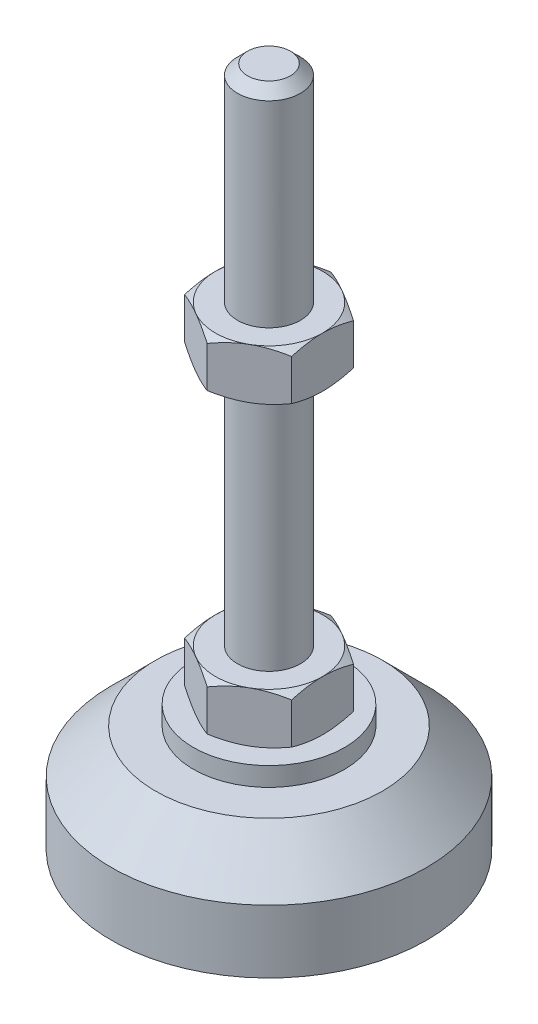
SolidWorks part; units mm, degrees
ref_plane "Спереди" through (0, 0, 0) normal (0, 0, 1) x (1, 0, 0)
ref_plane "Сверху" through (0, 0, 0) normal (0, 1, 0) x (1, 0, 0)
ref_plane "Справа" through (0, 0, 0) normal (1, 0, 0) x (0, 0, -1)
sketch "Эскиз1" plane through (0, 0, 0) normal (0, 0, 1) x (1, 0, 0)
  line L0 (0, 0) -> (-25, 0)
  line L3 (-25, 0) -> (-25, 10)
  line L5 (-12, 20) -> (-5, 20)
  line L12 (-5, 28) -> (-5, 106.4)
  line L13 (-5, 106.4) -> (-3.4, 108)
  line L14 (-3.4, 108) -> (0, 108)
  line L15 (0, 108) -> (0, 0) construction
  line L16 (-5, 20) -> (0, 20) construction
  line L17 (0, 0) -> (0, 108)
  line L18 (0, 0) -> (0, -7.9595) construction
  line L19 (-5, 28) -> (-5, 20)
  line L20 (-12, 20) -> (-12, 17)
  line L21 (-12, 17) -> (-18, 17)
  line L22 (-18, 17) -> (-25, 10)
  point P8 (-5, 67.2)
  point P23 (-8.5, 20)
  dimension "D1" = 10
  dimension "D2" = 20
  dimension "D3" = 8
  dimension "D4" = 50
  dimension "D5" = 5
  dimension "D6" = 1.6
  dimension "D7" = 45
  dimension "D8" = 24
  dimension "D10" = 80
  dimension "D11" = 10
  dimension "D12" = 45
  dimension "D13" = 3
revolve "Повернуть1" add sketch "Эскиз1" angle 360 about L17
sketch "Эскиз2" plane through (0, 20, 0) normal (0, 1, 0) x (1, 0, 0)
  line L1 (0, 9.815) -> (-8.5, 4.9075)
  line L2 (-8.5, 4.9075) -> (-8.5, -4.9075)
  line L3 (-8.5, -4.9075) -> (0, -9.815)
  line L4 (0, -9.815) -> (8.5, -4.9075)
  line L5 (8.5, -4.9075) -> (8.5, 4.9075)
  line L6 (8.5, 4.9075) -> (0, 9.815)
  circle A0 centre (0, 0) radius 8.5 construction
  dimension "D1" = 17
extrude "Бобышка-Вытянуть1" add sketch "Эскиз2" along normal up to vertex (8 mm away) up to point (-5, 28, 0)
ref_plane "Плоскость1" through (0, 67.2, 0) normal (0, 1, 0) x (1, 0, 0)
sketch "Эскиз3" plane through (0, 67.2, 0) normal (0, 1, 0) x (1, 0, 0)
  line L6 (8.5, 4.9075) -> (0, 9.815)
  line L7 (0, 9.815) -> (-8.5, 4.9075)
  line L8 (-8.5, 4.9075) -> (-8.5, -4.9075)
  line L9 (-8.5, -4.9075) -> (0, -9.815)
  line L10 (0, -9.815) -> (8.5, -4.9075)
  line L11 (8.5, -4.9075) -> (8.5, 4.9075)
  line L12 (8.5, 4.9075) -> (0, 9.815)
  line L13 (0, 9.815) -> (-8.5, 4.9075)
  line L14 (-8.5, 4.9075) -> (-8.5, -4.9075)
  line L15 (-8.5, -4.9075) -> (0, -9.815)
  line L16 (0, -9.815) -> (8.5, -4.9075)
  line L17 (8.5, -4.9075) -> (8.5, 4.9075)
  dimension "D1" = 0
extrude "Бобышка-Вытянуть2" add sketch "Эскиз3" along normal blind 8
sketch "Эскиз4" plane through (0, 0, 0) normal (0, 0, 1) x (1, 0, 0)
  line L0 (-8.5, 75.2) -> (-15.4282, 71.2)
  line L1 (-15.4282, 71.2) -> (-15.4282, 75.2)
  line L2 (-15.4282, 75.2) -> (-8.5, 75.2)
  line L3 (-15.4282, 71.2) -> (-8.5, 67.2)
  line L4 (50, 67.2) -> (-50, 67.2) construction
  line L5 (-8.5, 67.2) -> (-15.4282, 67.2)
  line L6 (-15.4282, 67.2) -> (-15.4282, 71.2)
  line L7 (-8.5, 75.2) -> (-8.5, 67.2) construction
  line L8 (-8.5, 28) -> (-15.4282, 28)
  line L9 (-15.4282, 28) -> (-15.4282, 24)
  line L10 (-15.4282, 24) -> (-8.5, 28)
  line L11 (-8.5, 20) -> (-15.4282, 24)
  line L12 (-15.4282, 24) -> (-15.4282, 20)
  line L13 (-15.4282, 20) -> (-8.5, 20)
  line L14 (0, 108) -> (0, 96.3793) construction
  dimension "D1" = 30
  dimension "D2" = 30
revolve "Вырез-Повернуть2" cut sketch "Эскиз4" angle 360 about L14
